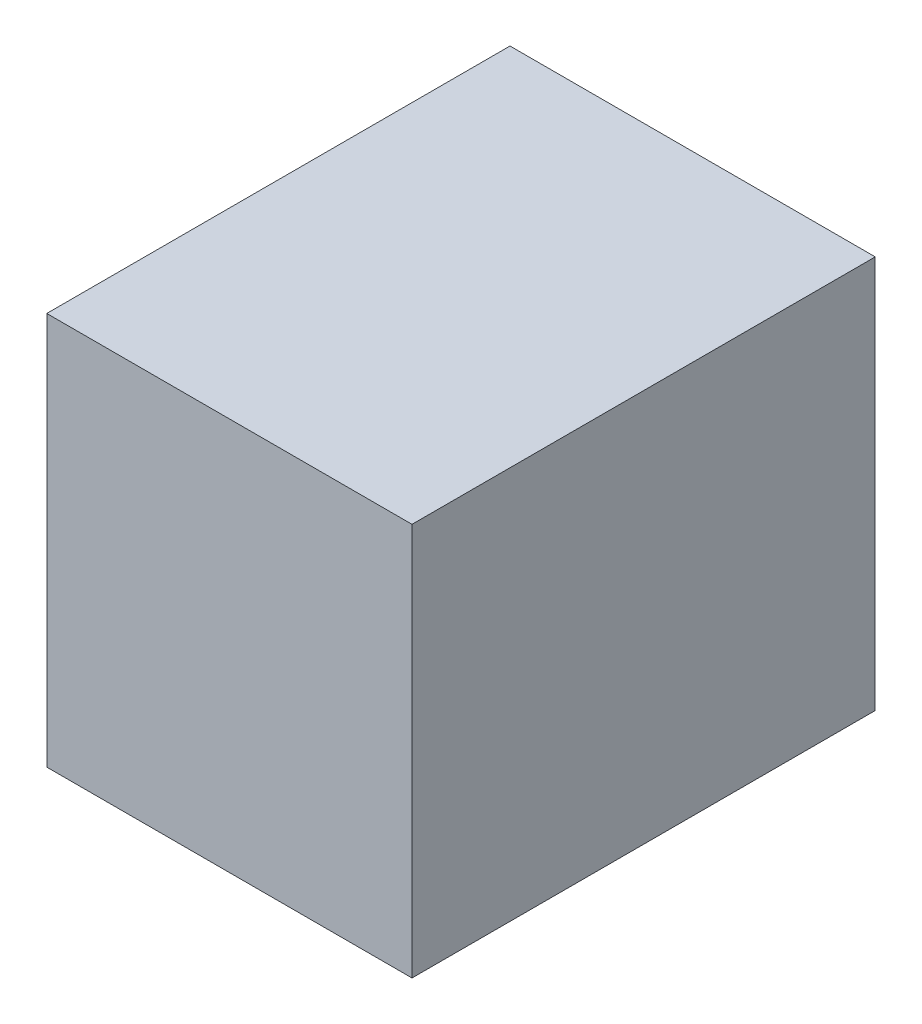
SolidWorks part; units mm, degrees
ref_plane "Front Plane" through (0, 0, 0) normal (0, 0, 1) x (1, 0, 0)
ref_plane "Top Plane" through (0, 0, 0) normal (0, 1, 0) x (1, 0, 0)
ref_plane "Right Plane" through (0, 0, 0) normal (1, 0, 0) x (0, 0, -1)
sketch "Sketch1" plane through (0, 0, 0) normal (0, 0, 1) x (1, 0, 0)
  line L1 (100, -110.5263) -> (-300, -110.5263)
  line L3 (100, 310.5263) -> (-300, 310.5263)
  line L4 (-300, -110.5263) -> (-300, 310.5263)
  line L6 (100, 100) -> (-300, 100) construction
  line L7 (-100, -110.5263) -> (-100, 310.5263) construction
  line L9 (0, 92.9289) -> (0, 100) construction
  line L10 (-14.1421, 200) -> (-185.8579, 0) construction
  line L11 (-210.0166, 210.0166) -> (10.0166, -10.0166) construction
  line L16 (100, 310.5263) -> (100, -110.5263)
  line L17 (0, 185.8579) -> (17.0876, 202.9455)
  line L18 (-14.1421, 200) -> (-185.8579, 200)
  line L19 (0, 14.1421) -> (0, 185.8579)
  line L20 (17.0876, -2.9455) -> (0, 14.1421)
  line L21 (-14.1421, 0) -> (2.9455, -17.0876)
  line L22 (-185.8579, 0) -> (-14.1421, 0)
  line L23 (-200, 185.8579) -> (-200, 14.1421)
  line L24 (0, 185.8579) -> (17.0876, 202.9455)
  line L25 (-202.9455, -17.0876) -> (-185.8579, 0)
  line L26 (-14.1421, 200) -> (-185.8579, 200) construction
  line L27 (0, 14.1421) -> (0, 185.8579) construction
  line L28 (17.0876, -2.9455) -> (0, 14.1421) construction
  line L29 (-14.1421, 0) -> (2.9455, -17.0876) construction
  line L30 (-185.8579, 0) -> (-14.1421, 0) construction
  line L31 (-200, 185.8579) -> (-200, 14.1421) construction
  line L32 (-202.9455, -17.0876) -> (-185.8579, 0)
  line L100 (-200, 14.1421) -> (-217.0876, -2.9455)
  line L101 (-200, 14.1421) -> (-217.0876, -2.9455)
  line L102 (-217.0876, 202.9455) -> (-200, 185.8579)
  line L103 (-217.0876, 202.9455) -> (-200, 185.8579)
  line L104 (-185.8579, 200) -> (-202.9455, 217.0876)
  line L105 (-185.8579, 200) -> (-202.9455, 217.0876)
  line L106 (2.9455, 217.0876) -> (-14.1421, 200)
  line L107 (2.9455, 217.0876) -> (-14.1421, 200)
  arc A2 (2.9455, -17.0876) -> (17.0876, -2.9455) centre (10.0166, -10.0166) ccw
  arc A3 (-217.0876, -2.9455) -> (-202.9455, -17.0876) centre (-210.0166, -10.0166) ccw
  arc A4 (2.9455, -17.0876) -> (17.0876, -2.9455) centre (10.0166, -10.0166) ccw construction
  arc A5 (-217.0876, -2.9455) -> (-202.9455, -17.0876) centre (-210.0166, -10.0166) ccw
  arc A24 (-202.9455, 217.0876) -> (-217.0876, 202.9455) centre (-210.0166, 210.0166) ccw
  arc A25 (-202.9455, 217.0876) -> (-217.0876, 202.9455) centre (-210.0166, 210.0166) ccw
  arc A26 (17.0876, 202.9455) -> (2.9455, 217.0876) centre (10.0166, 210.0166) ccw
  arc A27 (17.0876, 202.9455) -> (2.9455, 217.0876) centre (10.0166, 210.0166) ccw
  point P12 (-100, 100)
  point P26 (-100, 100)
  dimension "D3" = 0
extrude "Boss-Extrude1" add sketch "Sketch1" against normal blind 500
shell "Shell1" [suppressed] thickness 10
shell "Shell2" thickness 10
